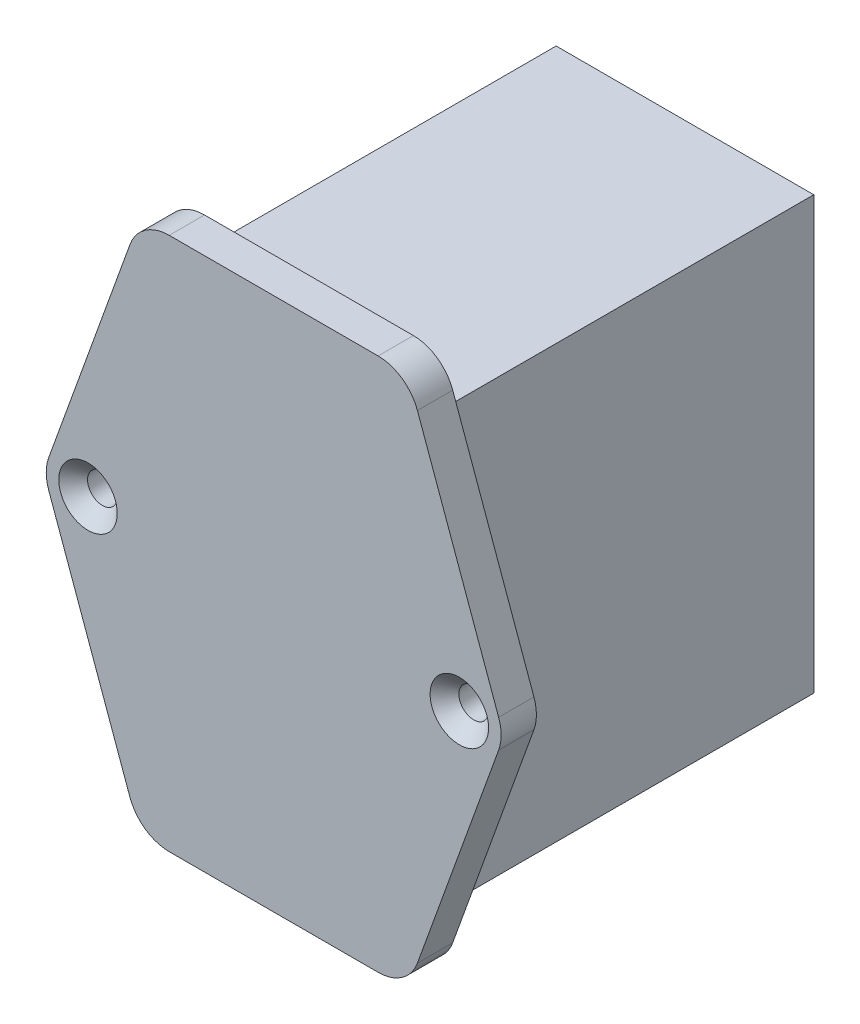
SolidWorks part; units mm, degrees
ref_plane "Front" through (0, 0, 0) normal (0, 0, 1) x (1, 0, 0)
ref_plane "Top" through (0, 0, 0) normal (0, 1, 0) x (1, 0, 0)
ref_plane "Right" through (0, 0, 0) normal (1, 0, 0) x (0, 0, -1)
sketch "Sketch1" plane through (0, 0, 0) normal (0, 0, 1) x (1, 0, 0)
  line L1 (0, 0) -> (27.75, 0)
  line L2 (0, 0) -> (0, 46.5)
  line L3 (0, 46.5) -> (27.75, 46.5)
  line L4 (27.75, 0) -> (27.75, 46.5)
  dimension "D1" = 27.75
  dimension "D2" = 46.5
extrude "Boss-Extrude1" add sketch "Sketch1" along normal blind 40.5
sketch "Sketch2" plane through (0, 0, 40.5) normal (0, 0, 1) x (1, 0, 0)
  line L0 (2.625, -5.2) -> (25.125, -5.2)
  line L1 (25.125, 52.3) -> (2.625, 52.3)
  line L2 (-1.6079, 49.3273) -> (-10.3579, 25.0773)
  line L3 (-10.3579, 22.0227) -> (-1.6079, -2.2273)
  line L4 (29.3579, -2.2273) -> (38.1079, 22.0227)
  line L5 (38.1079, 25.0773) -> (29.3579, 49.3273)
  line L6 (28.2853, 52.3) -> (28.2853, -5.2) construction
  line L7 (-0.5353, 52.3) -> (-0.5353, -5.2) construction
  line L8 (27.75, 46.5) -> (0, 46.5) construction
  line L9 (0, 46.5) -> (-0.5353, 46.5) construction
  line L10 (27.75, 46.5) -> (28.2853, 46.5) construction
  line L11 (38.659, 23.55) -> (28.2853, 23.55) construction
  line L12 (-0.5353, 23.55) -> (-10.909, 23.55) construction
  arc A0 (38.1079, 22.0227) -> (38.1079, 25.0773) centre (33.875, 23.55) ccw
  arc A1 (-10.3579, 25.0773) -> (-10.3579, 22.0227) centre (-6.125, 23.55) ccw
  circle A2 centre (-6.125, 23.55) radius 1.6
  circle A3 centre (33.875, 23.55) radius 1.6
  arc A4 (2.625, -5.2) -> (-1.6079, -2.2273) centre (2.625, -0.7) cw
  arc A5 (25.125, -5.2) -> (29.3579, -2.2273) centre (25.125, -0.7) ccw
  arc A6 (25.125, 52.3) -> (29.3579, 49.3273) centre (25.125, 47.8) cw
  arc A7 (2.625, 52.3) -> (-1.6079, 49.3273) centre (2.625, 47.8) ccw
  dimension "D3" = 4.5
  dimension "D4" = 3.2
  dimension "D5" = 40
  dimension "D6" = 4.5
  dimension "D1" = 57.5
  dimension "D2" = 5.8
  dimension "D7" = 22.5
extrude "Boss-Extrude2" add sketch "Sketch2" along normal blind 3.8
hole_wizard "CSK for M3 Flat Head Machine Screw1" positions "Sketch3" profile "Sketch4" countersink size "M3" standard "ANSI Metric" end condition through all
sketch "Sketch3" plane through (0, 0, 44.3) normal (0, 0, 1) x (1, 0, 0)
  point P0 (-6.125, 23.55)
  point P3 (33.875, 23.55)
sketch "Sketch4" plane through (-6.125, 23.55, 44.3) normal (1, 0, 0) x (0, -1, 0)
  line L0 (0, 0) -> (0, 44.3)
  line L1 (0, 44.3) -> (1.6, 44.3)
  line L2 (1.6, 44.3) -> (1.6, 1.55)
  line L3 (1.6, 1.55) -> (3.15, 0)
  line L5 (3.15, 0) -> (0, 0)
  line L6 (-1.6, 1.55) -> (-3.15, 0) construction
  line L11 (0, -6.35) -> (0, 107.95) construction
  dimension "Thru Hole Dia." = 3.2
  dimension "Thru Hole Depth" = 44.3
  dimension "Near C'Sink Dia." = 6.3
  dimension "Near C'Sink Angle" = 90
